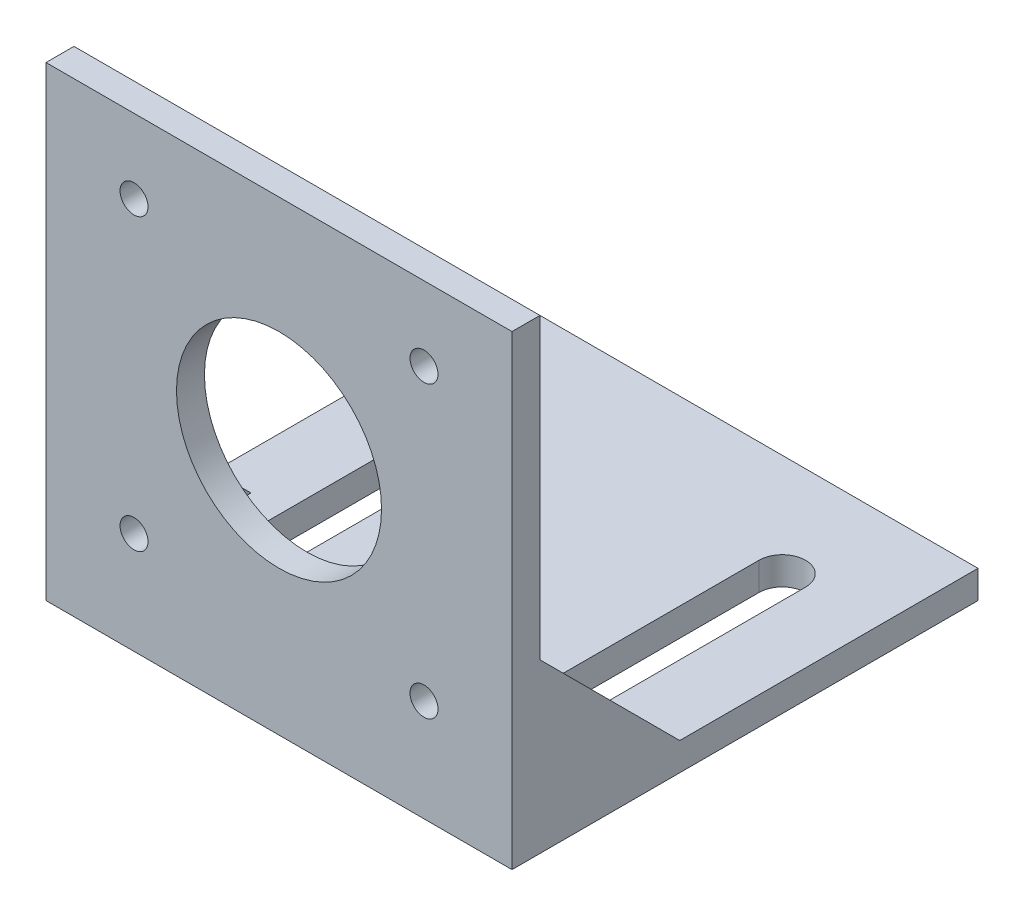
SolidWorks part; units mm, degrees
ref_plane "Front Plane" through (0, 0, 0) normal (0, 0, 1) x (1, 0, 0)
ref_plane "Top Plane" through (0, 0, 0) normal (0, 1, 0) x (1, 0, 0)
ref_plane "Right Plane" through (0, 0, 0) normal (1, 0, 0) x (0, 0, -1)
sketch "Sketch1" plane through (0, 0, 0) normal (1, 0, 0) x (0, 0, -1)
  line L0 (0, 0) -> (0, 50)
  line L1 (0, 0) -> (50, 0)
  line L2 (3, 3) -> (50, 3)
  line L3 (3, 3) -> (3, 50)
  line L4 (50, 0) -> (50, 3)
  line L5 (0, 50) -> (3, 50)
  dimension "D1" = 50
  dimension "D2" = 3
extrude "Boss-Extrude1" add sketch "Sketch1" along normal blind 50
sketch "Sketch3" plane through (0, 0, -3) normal (0, 0, -1) x (-1, 0, 0)
  line L0 (-50, 3) -> (-50, 50) construction
  line L1 (-50, 50) -> (0, 50) construction
  circle A0 centre (-25, 26.5) radius 11
  point P4 (-50, 26.5)
  point P7 (-25, 50)
  dimension "D1" = 22
extrude "Cut-Extrude1" cut sketch "Sketch3" against normal blind 20
sketch "Sketch4" plane through (0, 3, 0) normal (0, 1, 0) x (1, 0, 0)
  line L0 (10, 14) -> (10, 39) construction
  line L1 (7.5, 14) -> (7.5, 39)
  line L2 (12.5, 14) -> (12.5, 39)
  line L3 (0, 50) -> (0, 3) construction
  line L4 (25, 50) -> (25, 3) construction
  line L5 (50, 50) -> (0, 50) construction
  line L6 (50, 3) -> (0, 3) construction
  line L7 (40, 14) -> (40, 39) construction
  line L8 (42.5, 14) -> (42.5, 39)
  line L9 (37.5, 14) -> (37.5, 39)
  arc A0 (7.5, 14) -> (12.5, 14) centre (10, 14) ccw
  arc A1 (12.5, 39) -> (7.5, 39) centre (10, 39) ccw
  arc A2 (42.5, 14) -> (37.5, 14) centre (40, 14) cw
  arc A3 (37.5, 39) -> (42.5, 39) centre (40, 39) cw
  point P2 (10, 26.5)
  point P10 (0, 26.5)
  point P18 (40, 26.5)
  dimension "D1" = 25
  dimension "D2" = 30
  dimension "D3" = 5
extrude "Cut-Extrude2" cut sketch "Sketch4" against normal through all
sketch "Sketch5" plane through (0, 0, -3) normal (0, 0, -1) x (-1, 0, 0)
  line L1 (-10, 41.5) -> (-40, 41.5)
  line L2 (-10, 41.5) -> (-10, 11.5)
  line L3 (-10, 11.5) -> (-40, 11.5)
  line L4 (-40, 41.5) -> (-40, 11.5)
  line L5 (-10, 41.5) -> (-40, 11.5) construction
  line L6 (-10, 11.5) -> (-40, 41.5) construction
  point P0 (-25, 26.5)
  dimension "D1" = 30
sketch "Sketch6" plane through (50, 0, 0) normal (1, 0, 0) x (0, 0, -1)
  line L0 (3, 3) -> (18, 3)
  line L1 (50, 3) -> (3, 3) construction
  line L2 (18, 3) -> (3, 18)
  line L3 (3, 3) -> (3, 50) construction
  line L4 (3, 18) -> (3, 3)
  dimension "D1" = 15
extrude "Boss-Extrude2" add sketch "Sketch6" against normal blind 4
ref_plane "Plane1" through (25, 0, 0) normal (1, 0, 0) x (0, 0, -1)
mirror "Mirror1" about plane through (25, 0, 0) normal (1, 0, 0) of "Boss-Extrude2"
sketch "Sketch7" plane through (0, 0, -3) normal (0, 0, -1) x (-1, 0, 0)
  line L1 (-40.5563, 10.9437) -> (-9.4437, 10.9437) construction
  line L2 (-40.5563, 10.9437) -> (-40.5563, 42.0563) construction
  line L3 (-40.5563, 42.0563) -> (-9.4437, 42.0563) construction
  line L4 (-9.4437, 10.9437) -> (-9.4437, 42.0563) construction
  line L5 (-40.5563, 10.9437) -> (-9.4437, 42.0563) construction
  line L6 (-40.5563, 42.0563) -> (-9.4437, 10.9437) construction
  circle A0 centre (-25, 26.5) radius 22 construction
  circle A1 centre (-40.5563, 42.0563) radius 1.5
  circle A2 centre (-9.4437, 42.0563) radius 1.5
  circle A3 centre (-40.5563, 10.9437) radius 1.5
  circle A4 centre (-9.4437, 10.9437) radius 1.5
  dimension "D1" = 44
  dimension "D3" = 3
  dimension "D2" = 31.1127
extrude "Cut-Extrude3" cut sketch "Sketch7" against normal through all
